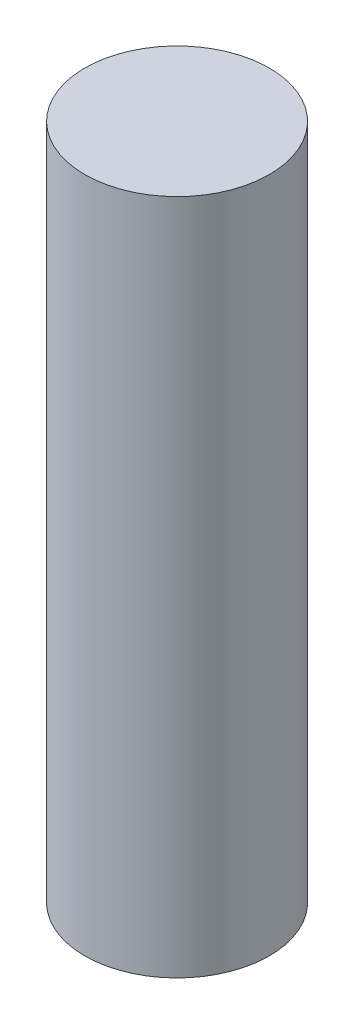
SolidWorks part; units mm, degrees
ref_plane "Front" through (0, 0, 0) normal (0, 0, 1) x (1, 0, 0)
ref_plane "Top" through (0, 0, 0) normal (0, 1, 0) x (1, 0, 0)
ref_plane "Right" through (0, 0, 0) normal (1, 0, 0) x (0, 0, -1)
sketch "Sketch1" plane through (0, 0, 0) normal (0, 1, 0) x (1, 0, 0)
  circle A0 centre (0, 0) radius 1.5
  dimension "D1" = 3
extrude "Boss-Extrude1" add sketch "Sketch1" along normal blind 11
